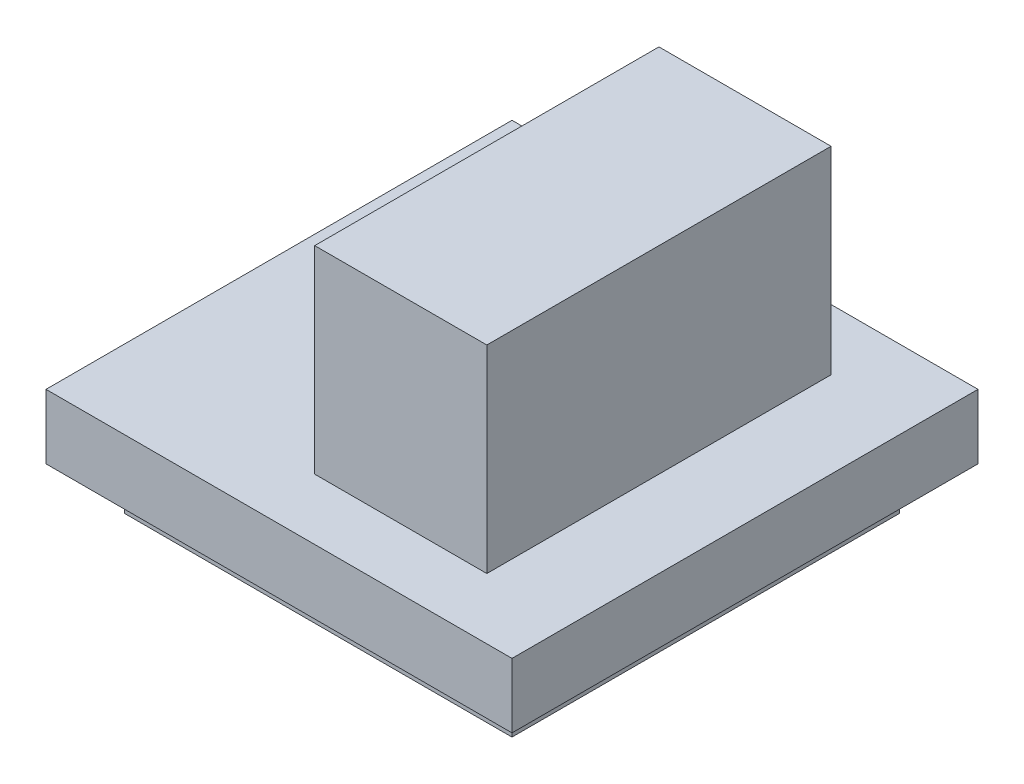
SolidWorks part; units mm, degrees
ref_plane "Front Plane" through (0, 0, 0) normal (0, 0, 1) x (1, 0, 0)
ref_plane "Top Plane" through (0, 0, 0) normal (0, 1, 0) x (1, 0, 0)
ref_plane "Right Plane" through (0, 0, 0) normal (1, 0, 0) x (0, 0, -1)
sketch "Sketch1" plane through (0, 0, 0) normal (0, 1, 0) x (1, 0, 0)
  line L1 (-5.415, -5.415) -> (5.415, -5.415)
  line L2 (-5.415, -5.415) -> (-5.415, 5.415)
  line L3 (-5.415, 5.415) -> (5.415, 5.415)
  line L4 (5.415, -5.415) -> (5.415, 5.415)
  line L5 (-5.415, -5.415) -> (5.415, 5.415) construction
  line L6 (-5.415, 5.415) -> (5.415, -5.415) construction
  point P0 (0, 0)
  dimension "D1" = 10.83
extrude "Extrude1" add sketch "Sketch1" along normal blind 1.5
sketch "Sketch2" plane through (0, 0, 0) normal (0, -1, 0) x (1, 0, 0)
  line L1 (4.5, 4.5) -> (-4.5, 4.5)
  line L2 (4.5, 4.5) -> (4.5, -4.5)
  line L3 (4.5, -4.5) -> (-4.5, -4.5)
  line L4 (-4.5, 4.5) -> (-4.5, -4.5)
  line L5 (4.5, 4.5) -> (-4.5, -4.5) construction
  line L6 (4.5, -4.5) -> (-4.5, 4.5) construction
  point P0 (0, 0)
  dimension "D1" = 9
extrude "Extrude2" add sketch "Sketch2" along normal blind 1
sketch "Sketch3" plane through (0, 1.5, 0) normal (0, 1, 0) x (1, 0, 0)
  line L0 (0, 0) -> (1.415, 0) construction
  line L1 (-0.585, -4) -> (3.415, -4)
  line L2 (-0.585, -4) -> (-0.585, 4)
  line L3 (-0.585, 4) -> (3.415, 4)
  line L4 (3.415, -4) -> (3.415, 4)
  line L5 (-0.585, -4) -> (3.415, 4) construction
  line L6 (-0.585, 4) -> (3.415, -4) construction
  line L7 (5.415, -5.415) -> (5.415, 5.415) construction
  point P0 (1.415, 0)
  dimension "D1" = 8
  dimension "D2" = 4
  dimension "D3" = 6
extrude "Extrude3" add sketch "Sketch3" along normal blind 4.6
sketch "Sketch4" plane through (0, -1, 0) normal (0, -1, 0) x (1, 0, 0)
  line L1 (-2.365, -1.51) -> (2.365, -1.51)
  line L2 (-2.365, -1.51) -> (-2.365, 1.51)
  line L3 (-2.365, 1.51) -> (2.365, 1.51)
  line L4 (2.365, -1.51) -> (2.365, 1.51)
  line L5 (-2.365, -1.51) -> (2.365, 1.51) construction
  line L6 (-2.365, 1.51) -> (2.365, -1.51) construction
  point P0 (0, 0)
  dimension "D1" = 4.73
  dimension "D2" = 3.02
